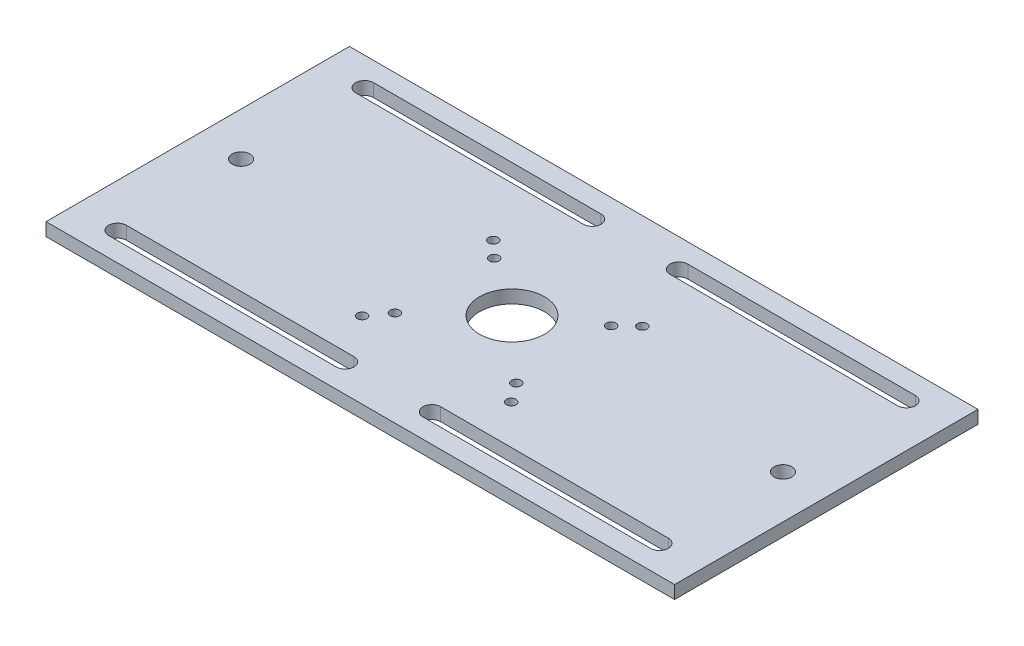
SolidWorks part; units mm, degrees
ref_plane "Спереди" through (0, 0, 0) normal (0, 0, 1) x (1, 0, 0)
ref_plane "Сверху" through (0, 0, 0) normal (0, 1, 0) x (1, 0, 0)
ref_plane "Справа" through (0, 0, 0) normal (1, 0, 0) x (0, 0, -1)
sketch "Эскиз1" plane through (0, 0, 0) normal (0, 1, 0) x (1, 0, 0)
  line L0 (0, 71.4287) -> (0, -61.4668) construction
  line L1 (-145, 70) -> (145, 70)
  line L2 (-145, 70) -> (-145, -70)
  line L3 (-145, -70) -> (145, -70)
  line L4 (145, 70) -> (145, -70)
  line L5 (-145, 70) -> (145, -70) construction
  line L6 (-145, -70) -> (145, 70) construction
  line L7 (-159.4957, 0) -> (166.2783, 0) construction
  line L8 (-163.7347, 57) -> (56.6685, 57) construction
  line L9 (-72.5, 92.4692) -> (-72.5, -67.0228) construction
  line L10 (-125, 61.1) -> (-20, 61.1)
  line L11 (-125, 52.9) -> (-20, 52.9)
  line L12 (-125, -52.9) -> (-20, -52.9)
  line L13 (-125, -61.1) -> (-20, -61.1)
  line L14 (125, -61.1) -> (20, -61.1)
  line L15 (125, -52.9) -> (20, -52.9)
  line L16 (125, 52.9) -> (20, 52.9)
  line L17 (125, 61.1) -> (20, 61.1)
  arc A0 (-125, 61.1) -> (-125, 52.9) centre (-125, 57) ccw
  arc A1 (-20, 61.1) -> (-20, 52.9) centre (-20, 57) cw
  arc A2 (-20, -61.1) -> (-20, -52.9) centre (-20, -57) ccw
  arc A3 (-125, -61.1) -> (-125, -52.9) centre (-125, -57) cw
  arc A4 (125, -61.1) -> (125, -52.9) centre (125, -57) ccw
  arc A5 (20, -61.1) -> (20, -52.9) centre (20, -57) cw
  arc A6 (20, 61.1) -> (20, 52.9) centre (20, 57) ccw
  arc A7 (125, 61.1) -> (125, 52.9) centre (125, 57) cw
  circle A8 centre (-125, 0) radius 4.1
  circle A9 centre (125, 0) radius 4.1
  circle A10 centre (0, 0) radius 15
  circle A11 centre (-34.4, 25.75) radius 2.2
  circle A12 centre (34.4, 25.75) radius 2.2
  circle A13 centre (-28, -26) radius 2.2
  circle A14 centre (-34.4, -34.75) radius 2.2
  circle A15 centre (-27, 18.75) radius 2.2
  circle A16 centre (28, -26) radius 2.2
  circle A17 centre (27, 18.75) radius 2.2
  circle A18 centre (34.4, -34.75) radius 2.2
  point P0 (0, 0)
  point P49 (34.4, 25.75)
  point P53 (-28, -26)
  point P57 (-34.4, -34.75)
  point P61 (-27, 18.75)
  point P67 (27, 18.75)
  point P69 (28, -26)
  point P73 (34.4, -34.75)
  dimension "D1" = 140
  dimension "D3" = 57
  dimension "D2" = 290
extrude "Бобышка-Вытянуть1" add sketch "Эскиз1" along normal blind 6
